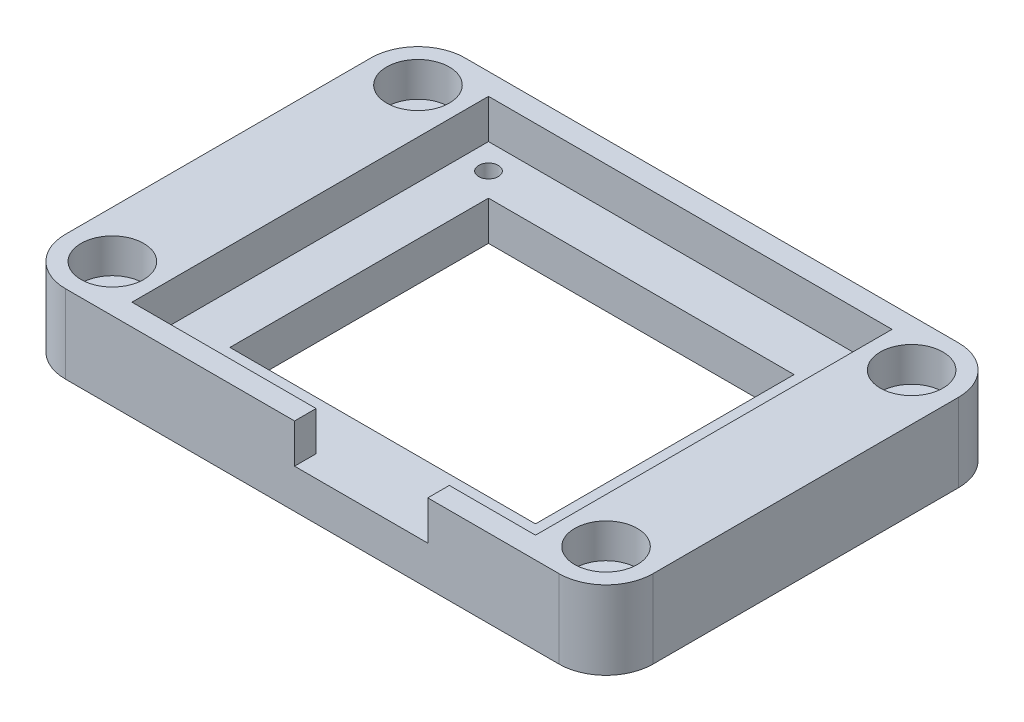
SolidWorks part; units mm, degrees
ref_plane "前视基准面" through (0, 0, 0) normal (0, 0, 1) x (1, 0, 0)
ref_plane "上视基准面" through (0, 0, 0) normal (0, 1, 0) x (1, 0, 0)
ref_plane "右视基准面" through (0, 0, 0) normal (1, 0, 0) x (0, 0, -1)
sketch "草图1" plane through (0, 0, 0) normal (0, 1, 0) x (1, 0, 0)
  line L1 (-37.5, -25.5) -> (37.5, -25.5)
  line L2 (-37.5, -25.5) -> (-37.5, 25.5)
  line L3 (-37.5, 25.5) -> (37.5, 25.5)
  line L4 (37.5, -25.5) -> (37.5, 25.5)
  line L5 (-37.5, -25.5) -> (37.5, 25.5) construction
  line L6 (-37.5, 25.5) -> (37.5, -25.5) construction
  point P1 (0, 0)
  dimension "D1" = 75
  dimension "D2" = 51
extrude "凸台-拉伸1" add sketch "草图1" along normal blind 10
sketch "草图2" plane through (0, 10, 0) normal (0, 1, 0) x (1, 0, 0)
  line L1 (-25.75, -22.75) -> (25.75, -22.75)
  line L2 (-25.75, -22.75) -> (-25.75, 22.75)
  line L3 (-25.75, 22.75) -> (25.75, 22.75)
  line L4 (25.75, -22.75) -> (25.75, 22.75)
  line L5 (-25.75, -22.75) -> (25.75, 22.75) construction
  line L6 (-25.75, 22.75) -> (25.75, -22.75) construction
  point P0 (0, 0)
  dimension "D1" = 51.5
  dimension "D2" = 45.5
extrude "切除-拉伸1" cut sketch "草图2" against normal blind 5
sketch "草图3" plane through (0, 5, 0) normal (0, 1, 0) x (1, 0, 0)
  line L1 (-22.5, -19.5) -> (22.5, -19.5) construction
  line L2 (-22.5, -19.5) -> (-22.5, 19.5) construction
  line L3 (-22.5, 19.5) -> (22.5, 19.5) construction
  line L4 (22.5, -19.5) -> (22.5, 19.5) construction
  line L5 (-22.5, -19.5) -> (22.5, 19.5) construction
  line L6 (-22.5, 19.5) -> (22.5, -19.5) construction
  circle A0 centre (-22.5, 19.5) radius 1.25
  circle A1 centre (-22.5, -19.5) radius 1.25
  circle A2 centre (22.5, -19.5) radius 1.25
  circle A3 centre (22.5, 19.5) radius 1.25
  point P0 (0, 0)
  dimension "D1" = 2.5
  dimension "D2" = 45
  dimension "D3" = 39
extrude "切除-拉伸2" cut sketch "草图3" against normal blind 5
sketch "草图4" plane through (0, 5, 0) normal (0, 1, 0) x (1, 0, 0)
  line L1 (-19.5, -16.5) -> (19.5, -16.5)
  line L2 (-19.5, -16.5) -> (-19.5, 16.5)
  line L3 (-19.5, 16.5) -> (19.5, 16.5)
  line L4 (19.5, -16.5) -> (19.5, 16.5)
  line L5 (-19.5, -16.5) -> (19.5, 16.5) construction
  line L6 (-19.5, 16.5) -> (19.5, -16.5) construction
  point P0 (0, 0)
  dimension "D1" = 39
  dimension "D2" = 33
extrude "切除-拉伸3" cut sketch "草图4" against normal up to next
fillet "圆角1" radius 6 4 edges at (-37.5, 5, -25.5) (37.5, 5, -25.5) (37.5, 5, 25.5) (-37.5, 5, 25.5)
sketch "草图5" plane through (0, 0, 0) normal (0, -1, 0) x (1, 0, 0)
  line L1 (-19.3246, 19.5) -> (-20.9123, 22.25)
  line L2 (-20.9123, 22.25) -> (-24.0877, 22.25)
  line L3 (-24.0877, 22.25) -> (-25.6754, 19.5)
  line L4 (-25.6754, 19.5) -> (-24.0877, 16.75)
  line L5 (-24.0877, 16.75) -> (-20.9123, 16.75)
  line L6 (-20.9123, 16.75) -> (-19.3246, 19.5)
  line L7 (25.6754, 19.5) -> (24.0877, 22.25)
  line L8 (24.0877, 22.25) -> (20.9123, 22.25)
  line L9 (20.9123, 22.25) -> (19.3246, 19.5)
  line L10 (19.3246, 19.5) -> (20.9123, 16.75)
  line L11 (20.9123, 16.75) -> (24.0877, 16.75)
  line L12 (24.0877, 16.75) -> (25.6754, 19.5)
  line L13 (-19.3246, -19.5) -> (-20.9123, -16.75)
  line L14 (-20.9123, -16.75) -> (-24.0877, -16.75)
  line L15 (-24.0877, -16.75) -> (-25.6754, -19.5)
  line L16 (-25.6754, -19.5) -> (-24.0877, -22.25)
  line L17 (-24.0877, -22.25) -> (-20.9123, -22.25)
  line L18 (-20.9123, -22.25) -> (-19.3246, -19.5)
  line L19 (25.6754, -19.5) -> (24.0877, -16.75)
  line L20 (24.0877, -16.75) -> (20.9123, -16.75)
  line L21 (20.9123, -16.75) -> (19.3246, -19.5)
  line L22 (19.3246, -19.5) -> (20.9123, -22.25)
  line L23 (20.9123, -22.25) -> (24.0877, -22.25)
  line L24 (24.0877, -22.25) -> (25.6754, -19.5)
  circle A0 centre (-22.5, 19.5) radius 2.75 construction
  circle A1 centre (22.5, 19.5) radius 2.75 construction
  circle A2 centre (-22.5, -19.5) radius 2.75 construction
  circle A3 centre (22.5, -19.5) radius 2.75 construction
  dimension "D1" = 5.5
extrude "切除-拉伸4" cut sketch "草图5" against normal blind 2
hole_wizard "M4 六角凹头螺钉的柱形沉头孔1" positions "3D草图1" profile "草图6" counterbore size "M4" standard "ISO" end condition through all
sketch3d "3D草图1"
  line L0 (31.5, 10, 19.5) -> (31.5, 0, 19.5) construction
  line L1 (31.5, 10, -19.5) -> (31.5, 0, -19.5) construction
  line L2 (-31.5, 10, -19.5) -> (-31.5, 0, -19.5) construction
  line L3 (-31.5, 10, 19.5) -> (-31.5, 0, 19.5) construction
  point P0 (31.5, 10, 19.5)
  point P4 (31.5, 10, -19.5)
  point P8 (-31.5, 10, -19.5)
  point P12 (-31.5, 10, 19.5)
sketch "草图6" plane through (31.5, 10, 19.5) normal (1, 0, 0) x (0, 0, 1)
  line L0 (0, 0) -> (0, 10)
  line L1 (0, 10) -> (2.25, 10)
  line L3 (2.25, 10) -> (2.25, 4.4)
  line L4 (2.25, 4.4) -> (4, 4.4)
  line L5 (4, 4.4) -> (4, 0)
  line L7 (4, 0) -> (0, 0)
  line L11 (0, -6.35) -> (0, 107.95) construction
  dimension "通孔孔直径" = 4.5
  dimension "通孔孔深度" = 10
  dimension "柱形沉头孔直径" = 8
  dimension "柱形沉头孔深度" = 4.4
sketch "草图7" plane through (0, 10, 0) normal (0, 1, 0) x (1, 0, 0)
  line L0 (-25.75, -22.75) -> (25.75, -22.75) construction
  line L1 (-2.25, -25.5) -> (14.75, -25.5)
  line L2 (-2.25, -25.5) -> (-2.25, -22.75)
  line L3 (-2.25, -22.75) -> (14.75, -22.75)
  line L4 (14.75, -25.5) -> (14.75, -22.75)
  line L5 (-2.25, -25.5) -> (14.75, -22.75) construction
  line L6 (-2.25, -22.75) -> (14.75, -25.5) construction
  line L7 (25.75, -22.75) -> (25.75, 22.75) construction
  line L8 (-31.5, -25.5) -> (31.5, -25.5) construction
  point P0 (6.25, -24.125)
  dimension "D1" = 19.5
  dimension "D2" = 17
extrude "切除-拉伸5" cut sketch "草图7" against normal up to surface (5 mm away) up to face at (0, 5, 0)
